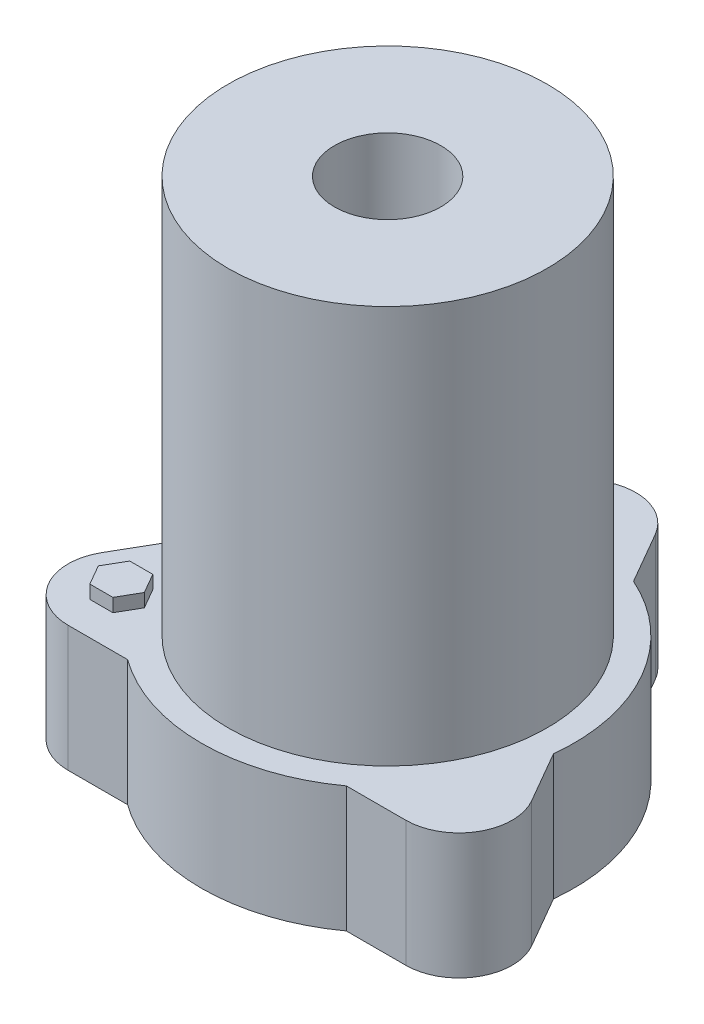
SolidWorks part; units mm, degrees
material "Chrome Stainless Steel"
ref_plane "Front Plane" through (0, 0, 0) normal (0, 0, 1) x (1, 0, 0)
ref_plane "Top Plane" through (0, 0, 0) normal (0, 1, 0) x (1, 0, 0)
ref_plane "Right Plane" through (0, 0, 0) normal (1, 0, 0) x (0, 0, -1)
sketch "Sketch1" plane through (0, 0, 0) normal (0, 1, 0) x (1, 0, 0)
  line L0 (-304.8, -609.6) -> (304.8, -609.6) construction
  line L1 (-184.15, -609.6) -> (304.8, -609.6) construction
  line L2 (-63.5, -609.6) -> (304.8, -609.6) construction
  line L3 (57.15, -609.6) -> (304.8, -609.6) construction
  line L4 (177.8, -609.6) -> (304.8, -609.6) construction
  line L5 (298.45, -609.6) -> (304.8, -609.6) construction
  line L6 (-88.4176, -9.2489) -> (-102.6195, -33.8474)
  line L7 (-80.6225, -71.9474) -> (-52.2186, -71.9474)
  line L8 (52.2186, -71.9474) -> (80.6225, -71.9474)
  line L9 (102.6195, -33.8474) -> (88.4176, -9.2489)
  line L10 (36.199, 81.1963) -> (21.997, 105.7948)
  line L11 (-21.997, 105.7948) -> (-36.199, 81.1963)
  line L12 (25.2005, 74.8463) -> (10.9985, 99.4448) construction
  line L14 (-10.9985, 99.4448) -> (-25.2005, 74.8463) construction
  line L15 (91.621, -40.1974) -> (77.4191, -15.5989) construction
  line L16 (52.2186, -59.2474) -> (80.6225, -59.2474) construction
  line L17 (-80.6225, -59.2474) -> (-52.2186, -59.2474) construction
  line L18 (-77.4191, -15.5989) -> (-91.621, -40.1974) construction
  arc A0 (-31.0277, 69.5969) -> (-75.7865, -7.9277) centre (0, 0) ccw
  circle A1 centre (-304.8, -609.6) radius 44.45 construction
  arc A2 (75.7865, -7.9277) -> (31.0277, 69.5969) centre (0, 0) ccw
  arc A3 (-44.7588, -61.6692) -> (44.7588, -61.6692) centre (0, 0) ccw
  circle A4 centre (-184.15, -609.6) radius 44.45 construction
  circle A5 centre (-63.5, -609.6) radius 44.45 construction
  circle A6 centre (57.15, -609.6) radius 44.45 construction
  circle A7 centre (177.8, -609.6) radius 44.45 construction
  circle A8 centre (298.45, -609.6) radius 44.45 construction
  arc A13 (-36.199, 81.1963) -> (-88.4176, -9.2489) centre (0, 0) ccw
  arc A14 (-88.4176, -9.2489) -> (-88.4176, -9.2489) centre (-88.4176, -9.2489) cw
  arc A15 (-102.6195, -33.8474) -> (-80.6225, -71.9474) centre (-80.6225, -46.5474) ccw
  arc A16 (-52.2186, -71.9474) -> (-52.2186, -71.9474) centre (-52.2186, -71.9474) ccw
  arc A17 (-52.2186, -71.9474) -> (52.2186, -71.9474) centre (0, 0) ccw
  arc A18 (52.2186, -71.9474) -> (52.2186, -71.9474) centre (52.2186, -71.9474) ccw
  arc A19 (80.6225, -71.9474) -> (102.6195, -33.8474) centre (80.6225, -46.5474) ccw
  arc A20 (88.4176, -9.2489) -> (88.4176, -9.2489) centre (88.4176, -9.2489) ccw
  arc A21 (88.4176, -9.2489) -> (36.199, 81.1963) centre (0, 0) ccw
  arc A22 (36.199, 81.1963) -> (36.199, 81.1963) centre (36.199, 81.1963) ccw
  arc A23 (-21.997, 105.7948) -> (21.997, 105.7948) centre (0, 93.0948) cw
  arc A24 (-36.199, 81.1963) -> (-36.199, 81.1963) centre (-36.199, 81.1963) ccw
  circle A25 centre (0, 0) radius 76.2
  arc A26 (25.2005, 74.8463) -> (31.0277, 69.5969) centre (36.199, 81.1963) ccw construction
  arc A27 (-10.9985, 99.4448) -> (10.9985, 99.4448) centre (0, 93.0948) cw construction
  arc A28 (-31.0277, 69.5969) -> (-25.2005, 74.8463) centre (-36.199, 81.1963) ccw construction
  arc A29 (75.7865, -7.9277) -> (77.4191, -15.5989) centre (88.4176, -9.2489) ccw construction
  arc A30 (80.6225, -59.2474) -> (91.621, -40.1974) centre (80.6225, -46.5474) ccw construction
  arc A31 (52.2186, -59.2474) -> (44.7588, -61.6692) centre (52.2186, -71.9474) ccw construction
  arc A32 (-44.7588, -61.6692) -> (-52.2186, -59.2474) centre (-52.2186, -71.9474) ccw construction
  arc A33 (-91.621, -40.1974) -> (-80.6225, -59.2474) centre (-80.6225, -46.5474) ccw construction
  arc A34 (-75.7865, -7.9277) -> (-77.4191, -15.5989) centre (-88.4176, -9.2489) cw construction
  point P20 (27.3505, 71.1224)
  point P25 (47.9185, -59.2474)
  point P30 (-75.269, -11.875)
  point P65 (0, -609.6)
  dimension "D1" = 152.4
  dimension "D2" = 609.6
  dimension "D5" = 88.9
  dimension "D4" = 609.6
  dimension "D3" = 12.7
  dimension "D6" = 6
extrude "Boss-Extrude1" add sketch "Sketch1" along normal blind 60 contours A23 L11 A13 L6 A15 L7 A17 L8 A19 L9 A21 L10 A25 A3 A0 A2
sketch "Sketch2" plane through (0, 60, 0) normal (0, 1, 0) x (1, 0, 0)
  line L1 (-69.6239, -46.5474) -> (-75.1232, -37.0224)
  line L2 (-75.1232, -37.0224) -> (-86.1217, -37.0224)
  line L3 (-86.1217, -37.0224) -> (-91.621, -46.5474)
  line L4 (-91.621, -46.5474) -> (-86.1217, -56.0724)
  line L5 (-86.1217, -56.0724) -> (-75.1232, -56.0724)
  line L6 (-75.1232, -56.0724) -> (-69.6239, -46.5474)
  circle A0 centre (-80.6225, -46.5474) radius 9.525 construction
  dimension "D1" = 19.05
extrude "Boss-Extrude2" add sketch "Sketch2" along normal blind 6.35
sketch "Sketch3" plane through (0, 0, 0) normal (0, -1, 0) x (1, 0, 0)
  circle A0 centre (0, 0) radius 76.2
extrude "Boss-Extrude3" add sketch "Sketch3" against normal blind 250
sketch "Sketch4" plane through (0, 250, 0) normal (0, 1, 0) x (1, 0, 0)
  circle A0 centre (0, 0) radius 25.4
extrude "Cut-Extrude1" cut sketch "Sketch4" against normal blind 50.8 contours A0
